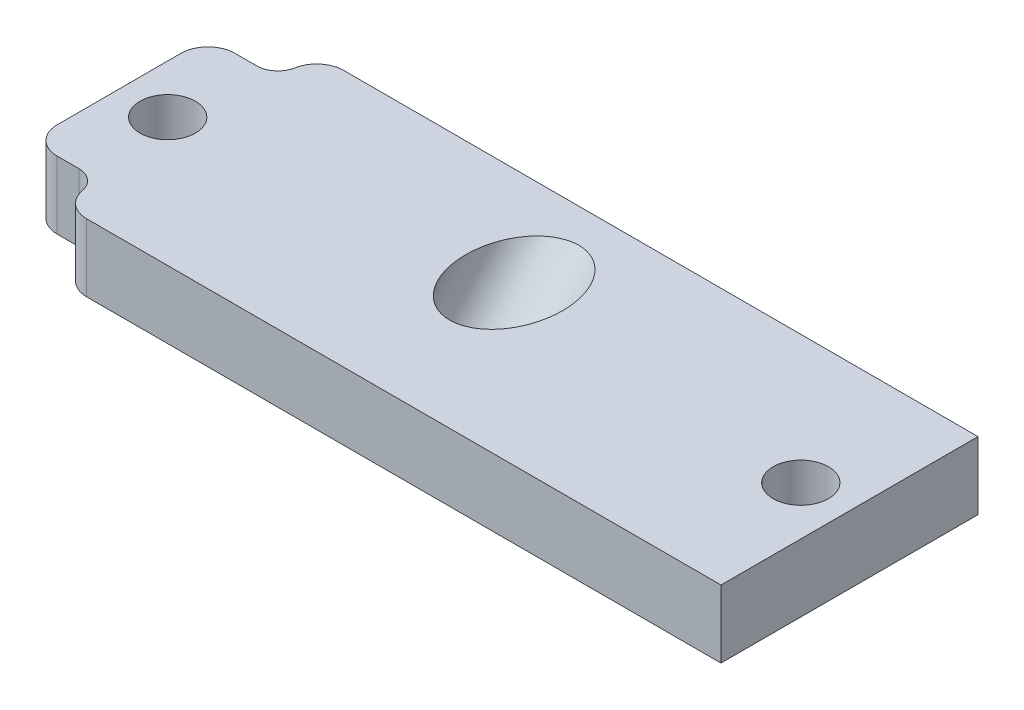
SolidWorks part; units mm, degrees
ref_plane "Front Plane" through (0, 0, 0) normal (0, 0, 1) x (1, 0, 0)
ref_plane "Top Plane" through (0, 0, 0) normal (0, 1, 0) x (1, 0, 0)
ref_plane "Right Plane" through (0, 0, 0) normal (1, 0, 0) x (0, 0, -1)
sketch "Sketch2" plane through (0, 0, 0) normal (0, 1, 0) x (1, 0, 0)
  line L1 (0, 0) -> (68.58, 0)
  line L2 (0, 0) -> (0, 24.13)
  line L3 (0, 24.13) -> (68.58, 24.13)
  line L4 (68.58, 0) -> (68.58, 24.13)
  circle A0 centre (4.57, 12.065) radius 2.6
  circle A1 centre (64.01, 12.065) radius 2.6
  point P10 (68.58, 12.065)
  dimension "D4" = 5.2
  dimension "D1" = 68.58
  dimension "D2" = 24.13
  dimension "D3" = 4.57
  dimension "D5" = 4.57
extrude "Boss-Extrude1" add sketch "Sketch2" along normal blind 6.35
sketch "Sketch3" plane through (0, 6.35, 0) normal (0, 1, 0) x (1, 0, 0)
  line L0 (6.57, 22.415) -> (6.57, 24.13)
  line L2 (4.57, 20.415) -> (0, 20.415)
  line L3 (0, 24.13) -> (0, 0) construction
  line L4 (68.58, 24.13) -> (0, 24.13) construction
  line L5 (4.57, 12.065) -> (64.01, 12.065) construction
  line L6 (34.29, 24.13) -> (34.29, 0) construction
  line L7 (0, 0) -> (68.58, 0) construction
  line L8 (6.57, 1.715) -> (6.57, 0)
  line L9 (4.57, 3.715) -> (0, 3.715)
  arc A0 (4.57, 20.415) -> (6.57, 22.415) centre (4.57, 22.415) ccw
  circle A1 centre (4.57, 12.065) radius 2.6 construction
  circle A2 centre (4.57, 12.065) radius 2.6
  arc A3 (4.57, 3.715) -> (6.57, 1.715) centre (4.57, 1.715) cw
  line M1 (0, 0) -> (68.58, 0)
  line M5 (68.58, 24.13) -> (0, 24.13)
  line M7 (0, 24.13) -> (0, 0)
  dimension "D1" = 10.35
  dimension "D2" = 4
extrude "Cut-Extrude1" cut sketch "Sketch3" against normal through all contours A3 L9 L8 M7 M1 | L2 A0 L0 M5 M7
fillet "Fillet3" radius 2.54 4 edges at (6.57, 3.175, 0) (0, 3.175, -3.715) (0, 3.175, -20.415) (6.57, 3.175, -24.13)
ref_plane "Plane1" through (0, 3.175, 0) normal (0, -1, 0) x (-1, 0, 0)
sketch "Sketch6" plane through (0, 3.175, 0) normal (0, -1, 0) x (-1, 0, 0)
  line L0 (-64.01, 12.065) -> (-4.57, 12.065) construction
  circle A0 centre (-4.57, 12.065) radius 2.6 construction
  circle A1 centre (-64.01, 12.065) radius 2.6 construction
  circle A2 centre (-4.57, 12.065) radius 2.6 construction
  circle A3 centre (-64.01, 12.065) radius 2.6 construction
ref_plane "Plane2" through (0, 7.7685, -6.873) normal (0, -0.749, 0.6626) x (-1, 0, 0)
sketch "Sketch7" plane through (0, 7.7685, -6.873) normal (0, -0.749, 0.6626) x (-1, 0, 0)
  line L0 (-64.01, 6.9323) -> (-4.57, 6.9323) construction
  line L1 (-64.01, 6.9323) -> (-4.57, 6.9323) construction
  circle A0 centre (-34.29, 6.9323) radius 4.55
  dimension "D1" = 9.1
extrude "Cut-Extrude2" cut sketch "Sketch7" against normal up to next and the other way up to next
